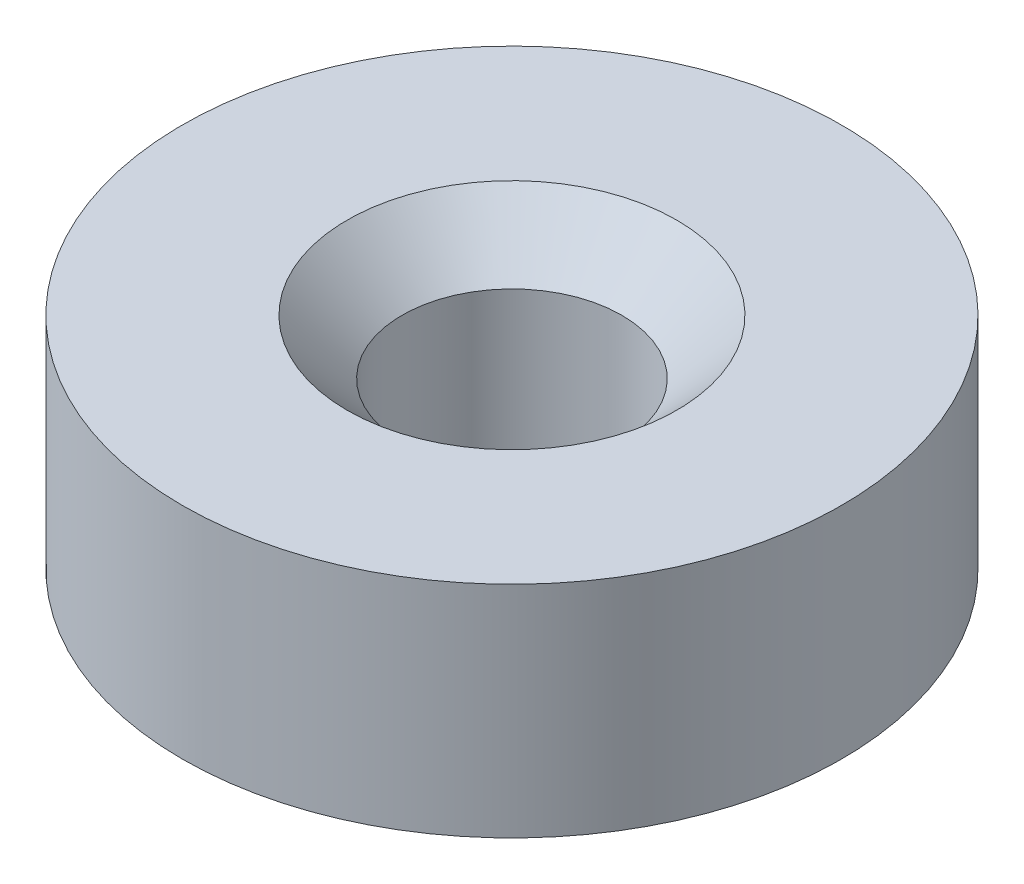
SolidWorks part; units mm, degrees
ref_plane "Front Plane" through (0, 0, 0) normal (0, 0, 1) x (1, 0, 0)
ref_plane "Top Plane" through (0, 0, 0) normal (0, 1, 0) x (1, 0, 0)
ref_plane "Right Plane" through (0, 0, 0) normal (1, 0, 0) x (0, 0, -1)
sketch "Sketch1" plane through (0, 0, 0) normal (0, 1, 0) x (1, 0, 0)
  circle A0 centre (0, 0) radius 2
  circle A1 centre (0, 0) radius 6
  dimension "D1" = 4
  dimension "D2" = 12
extrude "Boss-Extrude1" add sketch "Sketch1" along normal blind 4
chamfer "Chamfer1" distance 1 angle 45 1 edges at (0, 4, 2)
